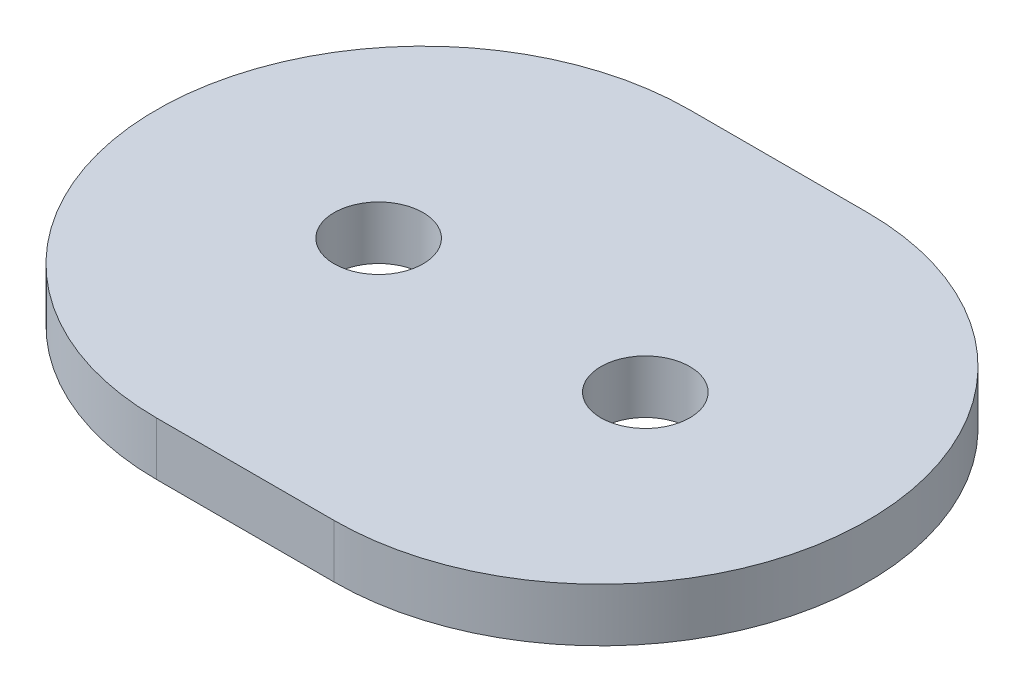
SolidWorks part; units mm, degrees
material "Plastique personnalisé"
ref_plane "Plan de face" through (0, 0, 0) normal (0, 0, 1) x (1, 0, 0)
ref_plane "Plan de dessus" through (0, 0, 0) normal (0, 1, 0) x (1, 0, 0)
ref_plane "Plan de droite" through (0, 0, 0) normal (1, 0, 0) x (0, 0, -1)
sketch "Esquisse2" plane through (0, 0, 0) normal (0, 1, 0) x (1, 0, 0)
  line L0 (-5, 0) -> (5, 0) construction
  line L1 (-5, 15) -> (5, 15)
  line L2 (-5, -15) -> (5, -15)
  arc A0 (-5, 15) -> (-5, -15) centre (-5, 0) ccw
  arc A1 (5, -15) -> (5, 15) centre (5, 0) ccw
  circle A2 centre (-7.5, 0) radius 2.5
  circle A3 centre (7.5, 0) radius 2.5
  point P3 (0, 0)
  dimension "D5" = 5
  dimension "D6" = 5
  dimension "D1" = 30
  dimension "D2" = 10
  dimension "D3" = 7.5
  dimension "D4" = 15
extrude "Boss.-Extru.1" add sketch "Esquisse2" along normal blind 3
